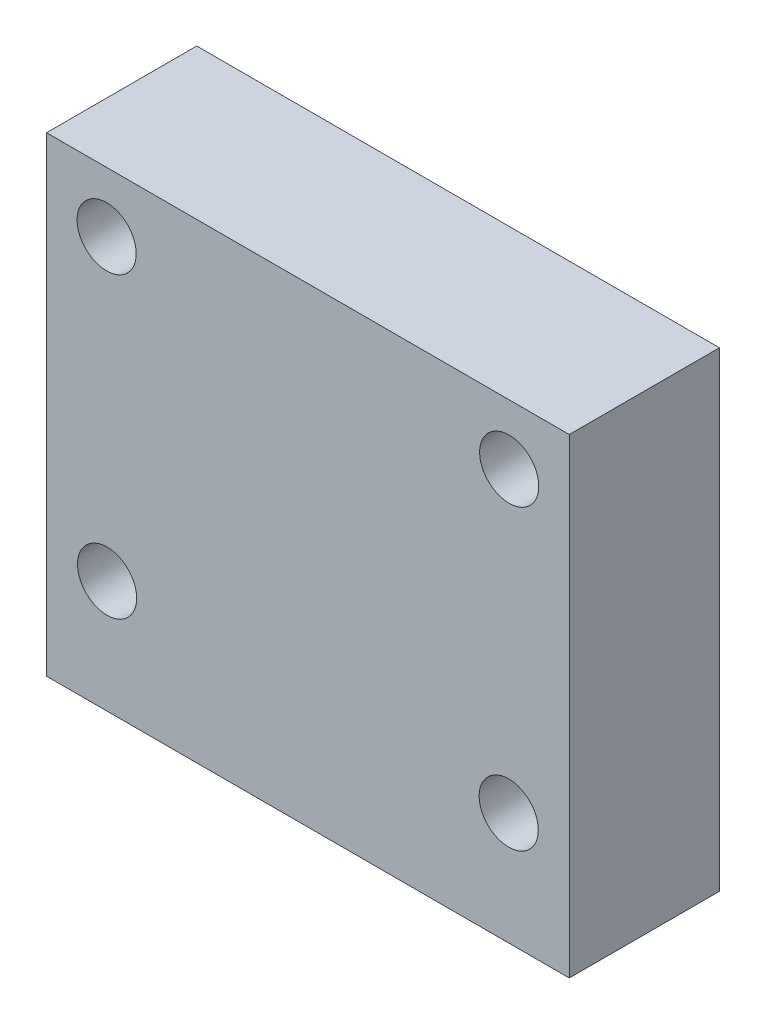
SolidWorks part; units mm, degrees
ref_plane "Front Plane" through (0, 0, 0) normal (0, 0, 1) x (1, 0, 0)
ref_plane "Top Plane" through (0, 0, 0) normal (0, 1, 0) x (1, 0, 0)
ref_plane "Right Plane" through (0, 0, 0) normal (1, 0, 0) x (0, 0, -1)
sketch "Sketch1" plane through (0, 0, 0) normal (0, 0, 1) x (1, 0, 0)
  line L1 (-11.05, -9.95) -> (11.05, -9.95)
  line L2 (-11.05, -9.95) -> (-11.05, 9.95)
  line L3 (-11.05, 9.95) -> (11.05, 9.95)
  line L4 (11.05, -9.95) -> (11.05, 9.95)
  line L5 (-11.05, -9.95) -> (11.05, 9.95) construction
  line L6 (-11.05, 9.95) -> (11.05, -9.95) construction
  point P0 (0, 0)
  dimension "D1" = 22.1
  dimension "D2" = 19.9
extrude "Extrude1" add sketch "Sketch1" along normal mid plane 6.35
sketch "Sketch2" plane through (0, -9.95, 0) normal (0, -1, 0) x (1, 0, 0)
  line L0 (-11.05, 3.175) -> (11.05, -3.175) construction
  circle A0 centre (0, 0) radius 1.0325
  dimension "D1" = 2.065
extrude "Extrude2" cut sketch "Sketch2" against normal blind 12.7
sketch "Sketch3" plane through (11.05, 0, 0) normal (1, 0, 0) x (0, 0, -1)
  line L0 (-3.175, 9.95) -> (-3.175, -9.95)
  line L1 (-3.175, -9.95) -> (-2.4801, 9.95)
  line L2 (-3.175, 9.95) -> (3.175, 9.95) construction
  line L3 (-2.4801, 9.95) -> (-3.175, 9.95)
  line L4 (0, 9.95) -> (0, -9.95) construction
  line L5 (-3.175, -9.95) -> (3.175, -9.95) construction
  line L6 (2.4801, 9.95) -> (3.175, 9.95)
  line L7 (3.175, -9.95) -> (2.4801, 9.95)
  line L8 (3.175, 9.95) -> (3.175, -9.95)
  dimension "D1" = 2
extrude "Extrude3" [suppressed] cut sketch "Sketch3" against normal through all
sketch "Sketch4" plane through (0, 0, 3.175) normal (0, 0, 1) x (1, 0, 0)
  circle A0 centre (8.49, -5.19) radius 1.25
  circle A1 centre (-8.51, 7.41) radius 1.25
  circle A2 centre (8.51, 7.41) radius 1.25
  circle A3 centre (-8.49, -5.19) radius 1.25
  dimension "D1" = 2.5
extrude "Cut-Extrude1" cut sketch "Sketch4" against normal through all
